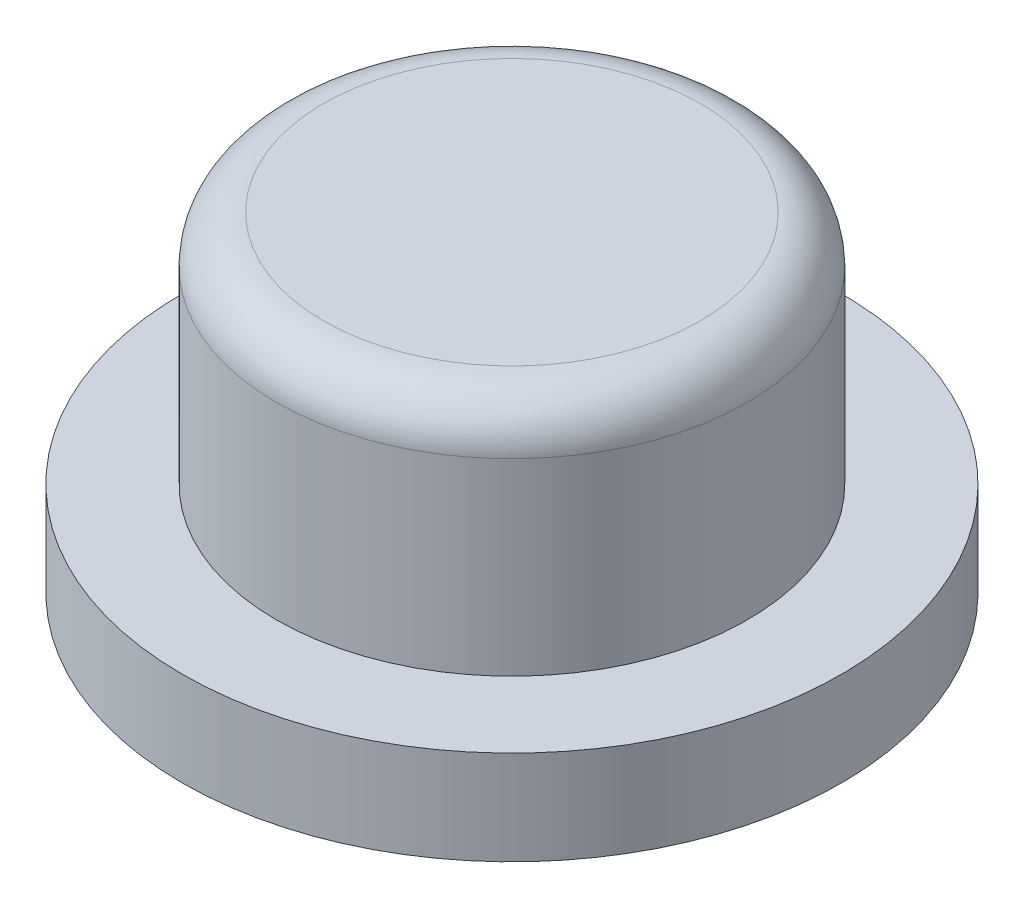
SolidWorks part; units mm, degrees
ref_plane "前视基准面" through (0, 0, 0) normal (0, 0, 1) x (1, 0, 0)
ref_plane "上视基准面" through (0, 0, 0) normal (0, 1, 0) x (1, 0, 0)
ref_plane "右视基准面" through (0, 0, 0) normal (1, 0, 0) x (0, 0, -1)
sketch "草图1" plane through (0, 0, 0) normal (0, 1, 0) x (1, 0, 0)
  circle A0 centre (0, 0) radius 7
  dimension "D1" = 14
extrude "凸台-拉伸1" add sketch "草图1" along normal blind 2
sketch "草图2" plane through (0, 2, 0) normal (0, 1, 0) x (1, 0, 0)
  circle A0 centre (0, 0) radius 5
  circle A1 centre (0, 0) radius 7 construction
  dimension "D1" = 2
extrude "凸台-拉伸2" add sketch "草图2" along normal blind 5
sketch "草图3" plane through (0, 0, 0) normal (0, -1, 0) x (1, 0, 0)
  circle A0 centre (0, 0) radius 2.5
  dimension "D1" = 5
extrude "切除-拉伸1" cut sketch "草图3" against normal blind 5
fillet "圆角1" radius 1 1 edges at (0, 7, 5)
